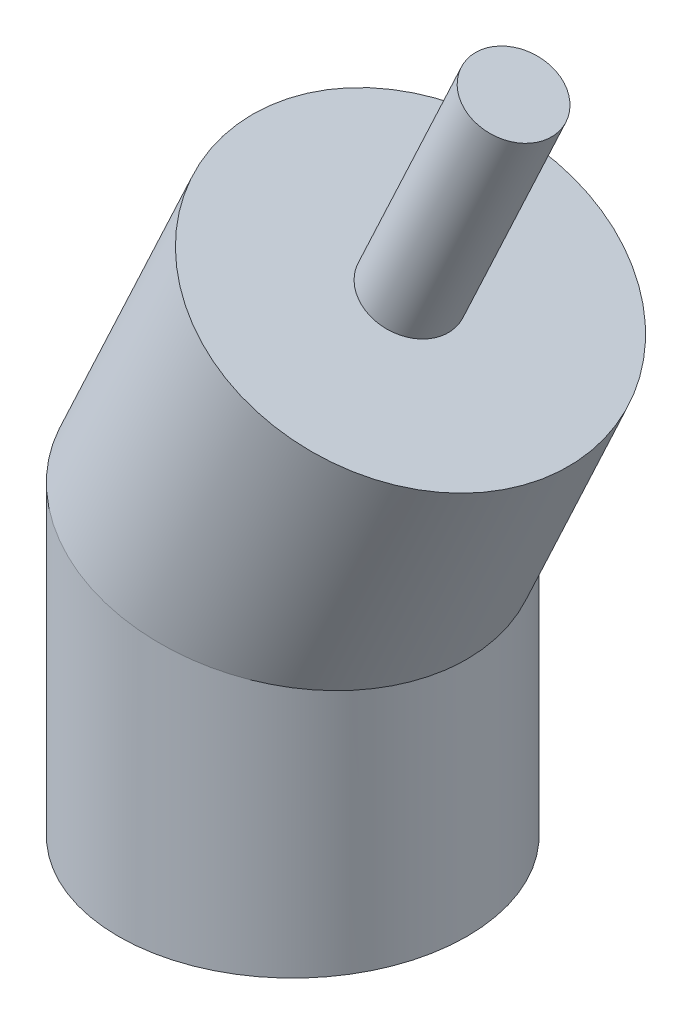
SolidWorks part; units mm, degrees
ref_plane "Plano frontal" through (0, 0, 0) normal (0, 0, 1) x (1, 0, 0)
ref_plane "Plano superior" through (0, 0, 0) normal (0, 1, 0) x (1, 0, 0)
ref_plane "Plano direito" through (0, 0, 0) normal (1, 0, 0) x (0, 0, -1)
sketch "Esboço1" plane through (0, 0, 0) normal (0, 0, 1) x (1, 0, 0)
  line L0 (16.9047, 76.2523) -> (0, 40)
  line L1 (0, 40) -> (0, 0)
  dimension "D1" = 25
  dimension "D2" = 40
  dimension "D3" = 40
sketch "Esboço2" plane through (0, 0, 0) normal (0, 1, 0) x (1, 0, 0)
  circle A0 centre (0, 0) radius 25
  dimension "D1" = 50
sweep "Varredura1" add profiles "Esboço2" path "Esboço1"
sketch "Esboço3" plane through (32.2256, 69.1081, 0) normal (0.4226, 0.9063, 0) x (0.9063, -0.4226, 0)
  line L0 (-16.9047, 0) -> (0, 0) construction
  circle A0 centre (-16.9047, 0) radius 6
  circle A1 centre (-16.9047, 0) radius 25 construction
  dimension "D1" = 12
extrude "Ressalto-extrusão1" add sketch "Esboço3" along normal blind 35
sketch "Esboço4" plane through (0, 0, 0) normal (0, -1, 0) x (1, 0, 0)
  circle A0 centre (0, 0) radius 6
  dimension "D1" = 12
extrude "Corte-extrusão1" cut sketch "Esboço4" against normal blind 20
